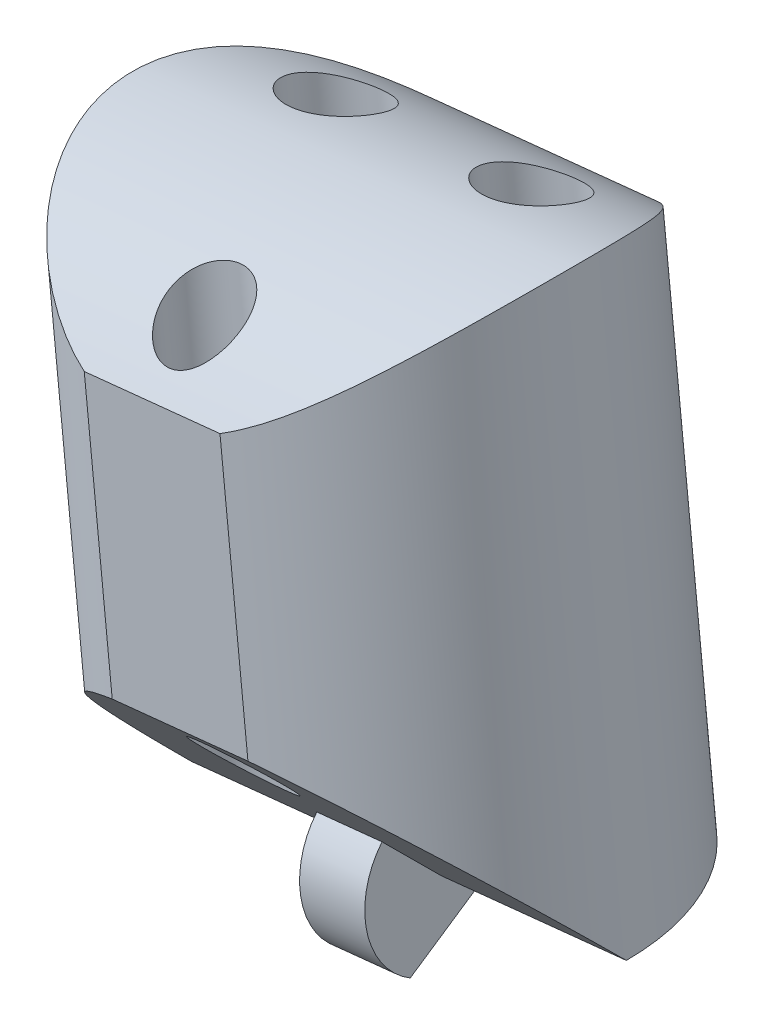
SolidWorks part; units mm, degrees
ref_plane "Front Plane" through (0, 0, 0) normal (0, 0, 1) x (1, 0, 0)
ref_plane "Top Plane" through (0, 0, 0) normal (0, 1, 0) x (1, 0, 0)
ref_plane "Right Plane" through (0, 0, 0) normal (1, 0, 0) x (0, 0, -1)
sketch "Sketch2" plane through (0, 0, 0) normal (0, 0, 1) x (1, 0, 0)
  line L0 (0, 0) -> (90, 0)
  line L1 (90, 0) -> (90, 120)
  line L2 (90, 120) -> (0, 120)
  line L3 (0, 120) -> (0, 0)
  line L4 (0, 120) -> (-10, 120)
  line L5 (-10, 120) -> (-10, 16.9491)
  line L6 (-10, 120) -> (57.5, 127)
  line L7 (57.5, 127) -> (90, 124)
  line L8 (90, 120) -> (99, 60)
  line L10 (90, 124) -> (90, 120)
  line L11 (5.9147, 0) -> (5.9147, -25)
  line L12 (5.9147, -25) -> (-4.0853, -25)
  line L13 (-4.0853, -29) -> (-4.0853, 0)
  line L14 (80, 0) -> (80, -25)
  line L15 (80, -25) -> (90, -25)
  line L16 (90, -29) -> (90, 0)
  line L17 (15.7927, 122.6748) -> (5.4776, 222.1414)
  line L18 (5.4776, 222.1414) -> (21.3923, 223.7918)
  line L19 (21.3923, 223.7918) -> (31.7073, 124.3252)
  line L20 (7.6492, 201.201) -> (23.5639, 202.8514)
  line L21 (10.9066, 169.7905) -> (26.8212, 171.441)
  line L22 (-10, 120) -> (-20.0396, 216.8108)
  line L23 (-20.0396, 216.8108) -> (-4.125, 218.4612)
  line L24 (-4.125, 218.4612) -> (5.9147, 121.6504)
  line L25 (-17.926, 196.4296) -> (-2.0114, 198.08)
  line L26 (-14.7556, 165.8578) -> (1.159, 167.5082)
  line L27 (57.5, 127) -> (46.9095, 229.1223)
  line L28 (46.9095, 229.1223) -> (30.9949, 227.4719)
  line L29 (30.9949, 227.4719) -> (41.5853, 125.3496)
  line L30 (33.2245, 205.9725) -> (49.1391, 207.6229)
  line L31 (36.5688, 173.7233) -> (52.4835, 175.3737)
  line L34 (90, 124) -> (99.1917, 223.5767)
  line L35 (99.1917, 223.5767) -> (83.2594, 225.0473)
  line L36 (83.2594, 225.0473) -> (74.0677, 125.4707)
  line L38 (81.3243, 204.0838) -> (97.2566, 202.6132)
  line L39 (78.4217, 172.6386) -> (94.354, 171.1679)
  line L40 (62.4078, 79.6749) -> (57.5, 127) construction
  line L41 (41.5853, 125.3496) -> (46.4931, 78.0244) construction
  line L42 (46.4931, 78.0244) -> (62.4078, 79.6749) construction
  line L43 (31.7073, 124.3252) -> (36.6151, 77.0001) construction
  line L44 (36.6151, 77.0001) -> (20.7005, 75.3496) construction
  line L45 (20.7005, 75.3496) -> (15.7927, 122.6748) construction
  line L46 (5.9147, 121.6504) -> (10.8224, 74.3253) construction
  line L47 (10.8224, 74.3253) -> (-5.0922, 72.6749) construction
  line L48 (-5.0922, 72.6749) -> (-10, 120) construction
  line L49 (74.0677, 125.4707) -> (69.6944, 78.0931) construction
  line L50 (69.6944, 78.0931) -> (85.7624, 78.0931) construction
  line L51 (85.7624, 78.0931) -> (90, 124) construction
  line L52 (-12.0823, 217.636) -> (10.4873, 0) construction
  line L53 (13.4349, 222.9666) -> (36.5574, 0) construction
  line L54 (38.9522, 228.2971) -> (62.6275, 0) construction
  line L55 (91.2256, 224.312) -> (70.5198, 0) construction
  line L59 (99, 60) -> (93.5277, 44.9649)
  line L60 (99, 60) -> (169.4769, 34.3485)
  line L61 (169.4769, 34.3485) -> (164.0046, 19.3134)
  line L62 (164.0046, 19.3134) -> (93.5277, 44.9649)
  line L63 (90, -2) -> (100, -2)
  line L64 (141.2862, 44.6091) -> (135.8138, 29.574)
  line L65 (99, 60) -> (55.7741, 75.7329) construction
  line L66 (55.7741, 75.7329) -> (50.3018, 60.6978) construction
  line L67 (100, -2) -> (100, -29)
  line L70 (-4.0853, -2) -> (-14.0853, -2)
  line L71 (-14.0853, -2) -> (-14.0853, -29)
  line L74 (-4.0853, 0) -> (0, 0)
  line L75 (-14.0853, -29) -> (-14.0853, -112.587)
  line L76 (-14.0853, -112.587) -> (100, -112.587)
  line L77 (100, -112.587) -> (100, -29)
  line L78 (-14.0853, -29) -> (100, -29)
  line L79 (-14.0853, -14.5) -> (100, -14.5) construction
  line L80 (31.7073, -112.587) -> (31.7073, -122.6232)
  line L81 (31.7073, -122.6232) -> (42.9573, -122.6232)
  line L82 (42.9573, -122.6232) -> (42.9573, -112.587)
  line L83 (-14.0853, -112.587) -> (-88.3667, -112.587)
  line L84 (-88.3667, -112.587) -> (-88.3667, -128.2699)
  line L85 (-88.3667, -128.2699) -> (169.4958, -128.2699)
  line L86 (169.4958, -128.2699) -> (169.4958, -112.587)
  line L87 (169.4958, -112.587) -> (100, -112.587)
  line L88 (90, 60) -> (-10, 60) construction
  line L89 (50.3018, 60.6978) -> (93.5277, 44.9649) construction
  line L90 (87.2806, 55.7521) -> (166.7408, 26.8309) construction
  line L91 (87.2806, 55.7521) -> (82.1749, 52.5336) construction
  line L92 (82.1749, 52.5336) -> (77.3257, 0) construction
  line L93 (83.1185, 56.6957) -> (86.337, 51.59) construction
  arc A0 (-10, 16.9491) -> (-4.0853, 0) centre (14.9876, 16.1624) ccw
  arc A1 (93.5277, 44.9649) -> (90, 0) centre (-126.4069, 39.5988) cw
  point P42 (41.1818, 206.7977)
  point P100 (84.7278, 54.1428)
  point P101 (84.7278, 54.1428)
  dimension "D11" = 47.3684
  dimension "D35" = 9
  dimension "D32" = 220
  dimension "D36" = 25
  dimension "D1" = 120
  dimension "D2" = 90
  dimension "D3" = 10
  dimension "D5" = 67.862
  dimension "D6" = 7
  dimension "D7" = 4
  dimension "D8" = 16
  dimension "D9" = 16
  dimension "D10" = 100
  dimension "D12" = 31.5789
  dimension "D13" = 16
  dimension "D14" = 16
  dimension "D15" = 16
  dimension "D16" = 25.7927
  dimension "D17" = 100
  dimension "D18" = 21.0526
  dimension "D19" = 31.5789
  dimension "D20" = 97.33
  dimension "D21" = 102.67
  dimension "D22" = 20.4905
  dimension "D23" = 30.7358
  dimension "D24" = 21.6147
  dimension "D25" = 32.4221
  dimension "D26" = 25
  dimension "D28" = 25
  dimension "D29" = 75
  dimension "D30" = 47.5789
  dimension "D31" = 30
  dimension "D33" = 46
  dimension "D34" = 20
  dimension "D37" = 2
  dimension "D38" = 2
  dimension "D39" = 27
  dimension "D40" = 10
  dimension "D41" = 10
  dimension "D42" = 27
  dimension "D43" = 14.5
  dimension "D44" = 127.5
ref_plane "Plane1" through (87.2806, 55.7521, 0) normal (-0.846, -0.5333, 0) x (0, 0, 1)
ref_plane "Plane2" through (82.1749, 52.5336, 0) normal (-0.0919, -0.9958, 0) x (-0.9958, 0.0919, 0)
ref_plane "Plane3" through (91.2256, 224.312, 0) normal (-0.0919, -0.9958, 0) x (-0.9958, 0.0919, 0)
ref_plane "Plane4" through (38.9522, 228.2971, 0) normal (0.1032, -0.9947, 0) x (-0.9947, -0.1032, 0)
ref_plane "Plane5" through (13.4349, 222.9666, 0) normal (0.1032, -0.9947, 0) x (-0.9947, -0.1032, 0)
ref_plane "Plane7" through (166.7408, 26.8309, 0) normal (0.9397, -0.342, 0) x (0, 0, -1)
ref_plane "Plane8" through (110.4217, -40.1902, 0) normal (0.9397, -0.342, 0) x (0, 0, -1)
ref_plane "Plane9" through (19.3664, 209.803, 0) normal (-0.0919, -0.9958, 0) x (-0.9958, 0.0919, 0)
ref_plane "Plane10" through (16.4638, 178.3578, 0) normal (-0.0919, -0.9958, 0) x (-0.9958, 0.0919, 0)
ref_plane "Plane11" through (-20.7793, 200.3721, 0) normal (0.1032, -0.9947, 0) x (-0.9947, -0.1032, 0)
ref_plane "Plane12" through (-17.435, 168.1229, 0) normal (0.1032, -0.9947, 0) x (-0.9947, -0.1032, 0)
ref_plane "Plane13" through (-20.5619, 198.2754, 0) normal (0.1032, -0.9947, 0) x (-0.9947, -0.1032, 0)
ref_plane "Plane14" through (-17.3045, 166.8649, 0) normal (0.1032, -0.9947, 0) x (-0.9947, -0.1032, 0)
ref_plane "Plane15" through (-12.0823, 217.636, 0) normal (0.1032, -0.9947, 0) x (-0.9947, -0.1032, 0)
ref_plane "Plane16" through (-20.3445, 196.1788, 0) normal (0.1032, -0.9947, 0) x (-0.9947, -0.1032, 0)
ref_plane "Plane17" through (-17.1741, 165.607, 0) normal (0.1032, -0.9947, 0) x (-0.9947, -0.1032, 0)
ref_plane "Plane18" through (12.1098, 131.1899, 0) normal (-0.0919, -0.9958, 0) x (-0.9958, 0.0919, 0)
ref_plane "Plane19" through (-12.4184, 119.7492, 0) normal (0.1032, -0.9947, 0) x (-0.9947, -0.1032, 0)
ref_plane "Plane20" through (0, 0, 0) normal (0, 0, 1) x (0.1032, -0.9947, 0)
ref_plane "Plane21" through (0, 0, 0) normal (0, 0, 1) x (-0.0919, -0.9958, 0)
ref_plane "Plane22" through (10.3758, 1.076, 0) normal (-0.9947, -0.1032, 0) x (0.1032, -0.9947, 0)
ref_plane "Plane23" through (36.1684, 3.7508, 0) normal (-0.9947, -0.1032, 0) x (0.1032, -0.9947, 0)
ref_plane "Plane24" through (61.9611, 6.4256, 0) normal (-0.9947, -0.1032, 0) x (0.1032, -0.9947, 0)
ref_plane "Plane25" through (69.924, -6.4545, 0) normal (-0.9958, 0.0919, 0) x (-0.0919, -0.9958, 0)
sketch "Sketch3" plane through (-12.0823, 217.636, 0) normal (0.1032, -0.9947, 0) x (-0.9947, -0.1032, 0)
  circle A0 centre (0, 0) radius 8
  dimension "D1" = 16
extrude "Boss-Extrude1" add sketch "Sketch3" along normal blind 21.0526
sketch "Sketch4" plane through (10.3758, 1.076, 0) normal (-0.9947, -0.1032, 0) x (0.1032, -0.9947, 0)
  line L0 (-217.7214, 8) -> (-213.7214, 8)
  line L1 (-196.6688, 8) -> (-217.7214, 8) construction
  line L2 (-217.7214, 8) -> (-217.7214, -8)
  line L3 (-217.7214, -8) -> (-213.7214, -8)
  line L4 (-217.7214, -8) -> (-196.6688, -8) construction
  arc A0 (-213.7214, 8) -> (-213.7214, -8) centre (-207.3937, 0) ccw
  dimension "D2" = 10.2
  dimension "D1" = 4
extrude "Cut-Extrude1" cut sketch "Sketch4" against normal through all and the other way through all
sketch "Sketch5" plane through (10.3758, 1.076, 0) normal (-0.9947, -0.1032, 0) x (0.1032, -0.9947, 0)
  line L0 (-196.6688, 0) -> (-204.6688, 8)
  line L1 (-196.6688, -8) -> (-196.6688, 8) construction
  line L2 (-196.6688, 8) -> (-213.7214, 8) construction
  line L3 (-204.6688, 8) -> (-196.6688, 8)
  line L4 (-196.6688, 8) -> (-196.6688, 0)
  dimension "D1" = 45
extrude "Cut-Extrude2" cut sketch "Sketch5" against normal through all and the other way through all
sketch "Sketch7" plane through (10.3758, 1.076, 0) normal (-0.9947, -0.1032, 0) x (0.1032, -0.9947, 0)
  line L11 (-198.6487, 1.9799) -> (-196.6688, 0)
  line L14 (-196.6688, 0) -> (-196.6688, -2.8)
  line L15 (-196.6688, -2.8) -> (-194.2439, 1.4)
  line L16 (-196.6688, 0) -> (-204.6688, 8) construction
  arc A0 (-198.6487, 1.9799) -> (-194.2439, 1.4) centre (-196.6688, 0) cw
  dimension "D2" = 2.8
  dimension "D1" = 30
  dimension "D3" = 2.8
extrude "Boss-Extrude3" add sketch "Sketch7" along normal mid plane 2.4
sketch "Sketch8" plane through (-12.0823, 217.636, 0) normal (0.1032, -0.9947, 0) x (-0.9947, -0.1032, 0)
  line L0 (8, 0) -> (-8, 0) construction
  circle A0 centre (-3.6, 3) radius 1.6
  circle A1 centre (3.6, 3) radius 1.6
  circle A3 centre (0, -5.5) radius 1.4
  point P6 (0, 0)
  dimension "D1" = 3.2
  dimension "D2" = 3.2
  dimension "D7" = 2.8
  dimension "D3" = 3
  dimension "D4" = 3
  dimension "D5" = 3.6
  dimension "D6" = 3.6
  dimension "D8" = 5.5
extrude "Cut-Extrude3" cut sketch "Sketch8" against normal through all and the other way through all
sketch "Sketch9" plane through (-20.2865, 195.6197, 0) normal (0.1032, -0.9947, 0) x (0.9947, 0.1032, 0)
  line L0 (7.9334, -7.6) -> (12.9294, -7.6)
  line L1 (2.4314, 0) -> (18.4314, 0) construction
  line L2 (7.9334, 7.6) -> (12.9294, 7.6)
  arc A0 (2.4314, 0) -> (18.4314, 0) centre (10.4314, 0) ccw construction
  arc A1 (7.9334, -7.6) -> (12.9294, -7.6) centre (10.4314, 0) ccw
  arc A2 (18.4314, 0) -> (2.4314, 0) centre (10.4314, 0) ccw construction
  arc A3 (7.9334, 7.6) -> (12.9294, 7.6) centre (10.4314, 0) cw
  point P14 (10.4314, 7.6)
  dimension "D1" = 7.6
  dimension "D2" = 7.6
extrude "Cut-Extrude4" cut sketch "Sketch9" against normal through all
